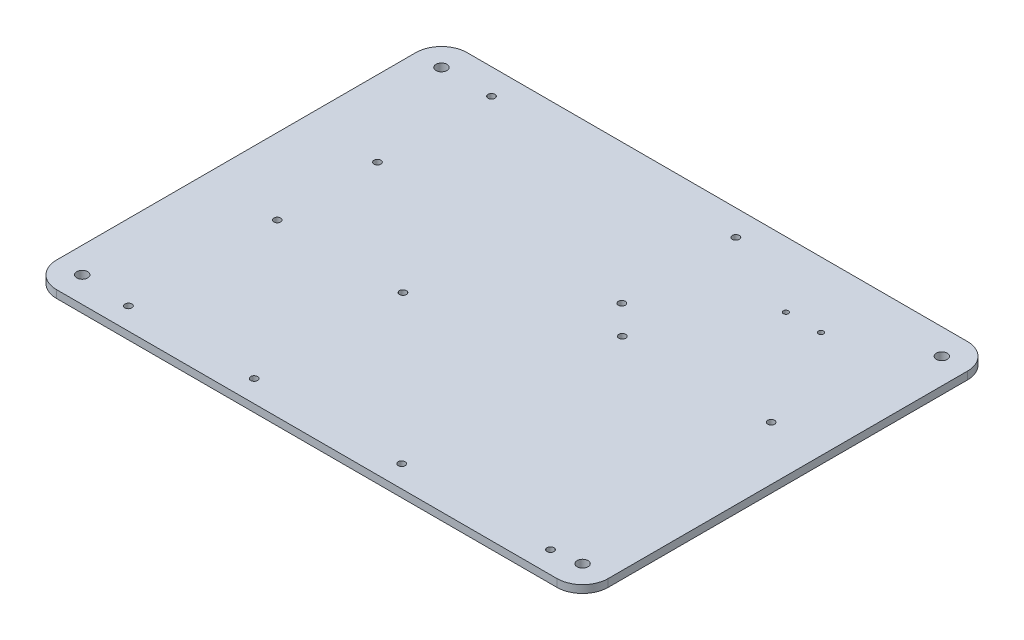
SolidWorks part; units mm, degrees
material "PP Copolymer"
ref_plane "Front Plane" through (0, 0, 0) normal (0, 0, 1) x (1, 0, 0)
ref_plane "Top Plane" through (0, 0, 0) normal (0, 1, 0) x (1, 0, 0)
ref_plane "Right Plane" through (0, 0, 0) normal (1, 0, 0) x (0, 0, -1)
sketch "Sketch1" plane through (0, 210, 0) normal (0, 1, 0) x (1, 0, 0)
  line L0 (-107.5, 102.5) -> (-107.5, -102.5) construction
  line L1 (-107.5, 80) -> (107.5, 80)
  line L2 (-107.5, 80) -> (-107.5, -80)
  line L3 (-107.5, -80) -> (107.5, -80)
  line L4 (107.5, 80) -> (107.5, -80)
  line L6 (107.5, 102.5) -> (107.5, -102.5) construction
  line L7 (-107.5, 80) -> (-107.5, 102.5) construction
  line L8 (-107.5, -80) -> (-107.5, -102.5) construction
  dimension "D1" = 160
extrude "Boss-Extrude1" add sketch "Sketch1" along normal blind 3
sketch "Sketch2" plane through (0, 213, 0) normal (0, 1, 0) x (1, 0, 0)
  line L0 (-107.5, -80) -> (107.5, -80) construction
  line L1 (-78.5, 10) -> (-28.5, 10) construction
  line L2 (-81.5, 7) -> (-81.5, -72) construction
  line L3 (-78.5, -75) -> (-28.5, -75) construction
  line L4 (-25.5, 7) -> (-25.5, -72) construction
  line L5 (-107.5, 80) -> (-107.5, -80) construction
  line L6 (107.5, 80) -> (-107.5, 80) construction
  line L7 (-78, -13.5) -> (-29, -13.5) construction
  line L8 (-78, -13.5) -> (-78, -71.5) construction
  line L9 (-78, -71.5) -> (-29, -71.5) construction
  line L10 (-29, -13.5) -> (-29, -71.5) construction
  line L11 (28.5, 14.5) -> (86.5, 14.5) construction
  line L12 (28.5, 14.5) -> (28.5, -71.5) construction
  line L13 (28.5, -71.5) -> (86.5, -71.5) construction
  line L14 (86.5, 14.5) -> (86.5, -71.5) construction
  line L15 (-78, 70) -> (17.25, 70) construction
  line L16 (-78, 70) -> (-78, 25.55) construction
  line L17 (-78, 25.55) -> (17.25, 25.55) construction
  line L18 (17.25, 70) -> (17.25, 25.55) construction
  line L19 (107.5, -80) -> (107.5, 80) construction
  line L20 (-97.5, 70) -> (97.5, 70) construction
  line L21 (-97.5, 70) -> (-97.5, -70) construction
  line L22 (-97.5, -70) -> (97.5, -70) construction
  line L23 (97.5, 70) -> (97.5, -70) construction
  arc A0 (-81.5, -72) -> (-78.5, -75) centre (-78.5, -72) ccw construction
  arc A1 (-28.5, -75) -> (-25.5, -72) centre (-28.5, -72) ccw construction
  arc A2 (-28.5, 10) -> (-25.5, 7) centre (-28.5, 7) cw construction
  arc A3 (-78.5, 10) -> (-81.5, 7) centre (-78.5, 7) ccw construction
  circle A4 centre (-78, -13.5) radius 1.35
  circle A5 centre (-29, -13.5) radius 1.35
  circle A6 centre (-29, -71.5) radius 1.35
  circle A7 centre (-78, -71.5) radius 1.35
  circle A8 centre (86.5, 14.5) radius 1.35
  circle A9 centre (86.5, -71.5) radius 1.35
  circle A10 centre (28.5, -71.5) radius 1.35
  circle A11 centre (28.5, 14.5) radius 1.35
  circle A12 centre (-78, 70) radius 1.35
  circle A13 centre (-78, 25.55) radius 1.35
  circle A14 centre (17.25, 25.55) radius 1.35
  circle A15 centre (17.25, 70) radius 1.35
  circle A16 centre (52.25, 54.5) radius 1
  circle A17 centre (65.95, 54.5) radius 1
  circle A18 centre (97.5, -70) radius 2.125
  circle A19 centre (97.5, 70) radius 2.125
  circle A20 centre (-97.5, 70) radius 2.125
  circle A21 centre (-97.5, -70) radius 2.125
  point P11 (-81.5, -75)
  point P16 (-25.5, 10)
  point P19 (-81.5, 10)
  dimension "D5" = 3
  dimension "D8" = 2.7
  dimension "D14" = 2.7
  dimension "D17" = 2.7
  dimension "D19" = 2
  dimension "D20" = 11.7
  dimension "D27" = 4.25
  dimension "D1" = 85
  dimension "D2" = 56
  dimension "D3" = 5
  dimension "D4" = 26
  dimension "D6" = 58
  dimension "D7" = 49
  dimension "D9" = 3.5
  dimension "D10" = 3.5
  dimension "D11" = 86
  dimension "D12" = 58
  dimension "D13" = 54
  dimension "D15" = 95.25
  dimension "D16" = 44.45
  dimension "D18" = 10
  dimension "D21" = 40
  dimension "D22" = 35
  dimension "D23" = 10
  dimension "D24" = 10
  dimension "D25" = 10
  dimension "D26" = 10
extrude "Cut-Extrude1" cut sketch "Sketch2" against normal through all
fillet "Fillet1" radius 10 4 edges at (-107.5, 211.5, 80) (107.5, 211.5, 80) (107.5, 211.5, -80) (-107.5, 211.5, -80)
